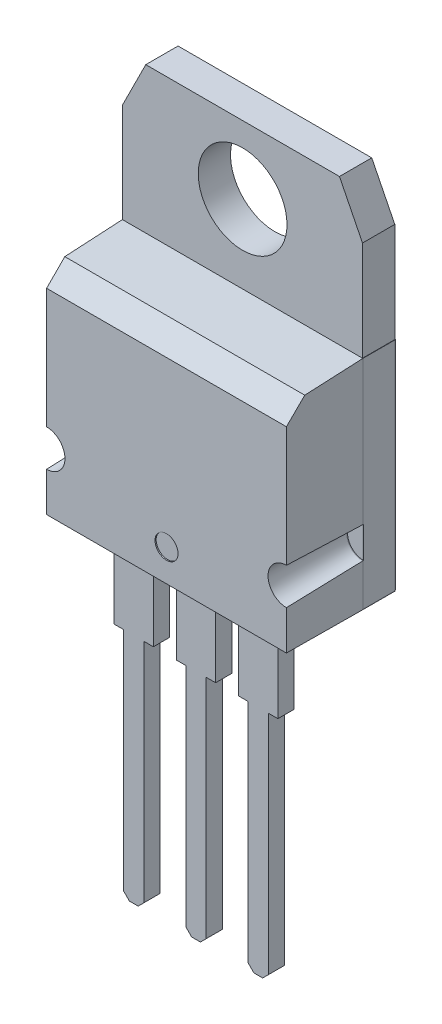
SolidWorks part; units mm, degrees
ref_plane "Front Plane" through (0, 0, 0) normal (0, 0, 1) x (1, 0, 0)
ref_plane "Top Plane" through (0, 0, 0) normal (0, 1, 0) x (1, 0, 0)
ref_plane "Right Plane" through (0, 0, 0) normal (1, 0, 0) x (0, 0, -1)
sketch "Sketch1" plane through (0, 0, 0) normal (0, 0, 1) x (1, 0, 0)
  line L0 (-5.2, 8.9352) -> (-4.2, 10.9352)
  line L1 (-4.2, 10.9352) -> (4.2, 10.9352)
  line L2 (-5.2, 8.9352) -> (-5.2, -4.8148)
  line L3 (-5.2, -4.8148) -> (5.2, -4.8148)
  line L4 (5.2, 8.9352) -> (5.2, -4.8148)
  line L5 (4.2, 10.9352) -> (5.2, 8.9352)
  circle A0 centre (0, 7.9852) radius 1.925
  point P0 (0, 0)
  point P2 (-5.2, 10.9352)
  point P4 (5.2, 10.9352)
  point P12 (0, -4.8148)
  dimension "D1" = 3.85
  dimension "D2" = 10.4
  dimension "D3" = 2.95
  dimension "D4" = 15.75
  dimension "D5" = 1
  dimension "D6" = 2
  dimension "D7" = 1
  dimension "D8" = 2
extrude "Boss-Extrude1" add sketch "Sketch1" along normal blind 1.4
sketch "Sketch2" plane through (0, 0, 1.4) normal (0, 0, 1) x (1, 0, 0)
  line L0 (5.2, -4.8148) -> (5.2, 8.9352) construction
  line L1 (-5.2, -4.8148) -> (5.2, -4.8148)
  line L2 (-5.2, -4.8148) -> (-5.2, 4.4352)
  line L3 (-5.2, 4.4352) -> (5.2, 4.4352)
  line L4 (5.2, -4.8148) -> (5.2, 4.4352)
  dimension "D1" = 9.25
extrude "Boss-Extrude2" add sketch "Sketch2" along normal blind 3.3 separate body
chamfer "Chamfer1" distance 0.75 angle 45 1 edges at (0, 4.4352, 4.7)
draft "Draft7" type of draft neutral plane draft angle 3 faces to draft 1 face at (0, 4.4352, 2.675) neutral plane through (0, 0, 4.7) neutral plane normal (0, 0, 1) parameters "D1"=3
draft "Draft8" type of draft neutral plane draft angle 0.25 faces to draft 2 face at (5.2, 0.6281, 3.2217) face at (-5.2, 0.6281, 3.2217) neutral plane through (0, 0, 4.7) neutral plane normal (0, 0, 1) parameters "D1"=0.25
sketch "Sketch4" plane through (0, 0, 1.4) normal (0, 0, -1) x (-1, 0, 0)
  line L0 (5.2144, -4.8148) -> (-5.2144, -4.8148) construction
  line L1 (-5.2144, 4.6082) -> (-5.2, 4.6082)
  line L2 (-5.2144, 4.6082) -> (-5.2144, -4.8148)
  line L3 (-5.2144, -4.8148) -> (-5.2, -4.8148)
  line L4 (-5.2, 4.6082) -> (-5.2, -4.8148)
  line L5 (5.2144, 4.6082) -> (5.2, 4.6082)
  line L6 (5.2144, 4.6082) -> (5.2144, -4.8148)
  line L7 (5.2144, -4.8148) -> (5.2, -4.8148)
  line L8 (5.2, 4.6082) -> (5.2, -4.8148)
  line L9 (5.2, 8.9352) -> (5.2, -4.8148) construction
extrude "Boss-Extrude4" add sketch "Sketch4" along normal up to surface (1.4 mm away) separate body up to face at (0, 5.0186, 0)
sketch "Sketch5" plane through (0, 0, 4.7) normal (0, 0, 1) x (1, 0, 0)
  line L0 (-5.2, 3.6852) -> (-5.2, -4.8148) construction
  line L1 (-5.2, -4.8148) -> (5.2, -4.8148) construction
  line L2 (0, -4.8148) -> (0, -1.5006) construction
  circle A0 centre (-5.2, -2.3148) radius 0.7956
  circle A1 centre (5.2, -2.3148) radius 0.7956
  dimension "D1" = 2.5
extrude "Cut-Extrude1" cut sketch "Sketch5" against normal blind 3.33 draft 2
sketch "Sketch6" plane through (0, 0, 0) normal (0, 0, -1) x (-1, 0, 0)
  line L0 (0, -4.8148) -> (0, 3.5396) construction
  line L1 (5.2, -4.8148) -> (-5.2, -4.8148) construction
  line L2 (-5.2, 4.6082) -> (-2.5164, 4.6082)
  line L3 (5.2, 4.6082) -> (2.5164, 4.6082)
  line L4 (-2.5164, 4.6082) -> (-2.5164, 3.8582)
  line L5 (2.5164, 4.6082) -> (2.5164, 3.8582)
  line L6 (-2.5164, 3.8582) -> (-3.7, 3.8582)
  line L7 (2.5164, 3.8582) -> (3.7, 3.8582)
  line L8 (-3.7, 3.8582) -> (-3.7, -2.2073)
  line L9 (3.7, 3.8582) -> (3.7, -2.2073)
  line L10 (-3.7, -2.2073) -> (-4.45, -2.2073)
  line L11 (3.7, -2.2073) -> (4.45, -2.2073)
  line L12 (-4.45, -2.2073) -> (-4.45, -3.0398)
  line L13 (4.45, -2.2073) -> (4.45, -3.0398)
  line L14 (-4.45, -3.0398) -> (-4.45, -3.0648)
  line L15 (4.45, -3.0398) -> (4.45, -3.0648)
  line L16 (-4.45, -3.0648) -> (-4.3106, -3.0648)
  line L17 (4.45, -3.0648) -> (4.3106, -3.0648)
  line L18 (-4.3106, -3.0648) -> (4.3106, -3.0648)
  line L19 (-5.2, 4.6082) -> (-5.2, -4.8148) construction
  line L20 (-5.2, 4.6082) -> (-5.2, -4.8148)
  line L21 (5.2, 4.6082) -> (5.2, -4.8148)
  line L22 (-5.2, -4.8148) -> (5.2, -4.8148)
  point P23 (0, -3.0648)
  dimension "D1" = 0.75
  dimension "D2" = 1.5
  dimension "D3" = 0.75
  dimension "D4" = 1.75
extrude "Boss-Extrude6" add sketch "Sketch6" along normal blind 0.025 separate body
ref_plane "Plane1" through (0, 0, 2.72) normal (0, 0, -1) x (-1, 0, 0)
sketch "Sketch10" plane through (0, 0, 2.72) normal (0, 0, -1) x (-1, 0, 0)
  line L0 (-0.85, -4.8148) -> (0.85, -4.8148)
  line L1 (-0.85, -4.8148) -> (-0.85, -8.7448)
  line L2 (-0.85, -8.7448) -> (-0.44, -8.7448)
  line L3 (0.85, -4.8148) -> (0.85, -8.7448)
  line L4 (-0.44, -8.7448) -> (-0.44, -18.5648)
  line L5 (-0.19, -18.8148) -> (0.19, -18.8148)
  line L6 (0.44, -18.5648) -> (0.44, -8.7448)
  line L7 (0.44, -8.7448) -> (0.85, -8.7448)
  line L8 (-0.44, -18.5648) -> (-0.19, -18.8148)
  line L9 (0.19, -18.8148) -> (0.44, -18.5648)
  line L10 (1.85, -4.8148) -> (1.85, -8.7448)
  line L11 (1.85, -4.8148) -> (3.55, -4.8148)
  line L12 (3.55, -4.8148) -> (3.55, -8.7448)
  line L13 (3.14, -8.7448) -> (3.55, -8.7448)
  line L14 (1.85, -8.7448) -> (2.26, -8.7448)
  line L15 (2.26, -8.7448) -> (2.26, -18.5648)
  line L16 (3.14, -18.5648) -> (3.14, -8.7448)
  line L17 (2.26, -18.5648) -> (2.51, -18.8148)
  line L18 (2.51, -18.8148) -> (2.89, -18.8148)
  line L19 (2.89, -18.8148) -> (3.14, -18.5648)
  line L20 (-3.55, -4.8148) -> (-3.55, -8.7448)
  line L21 (-3.55, -4.8148) -> (-1.85, -4.8148)
  line L22 (-1.85, -4.8148) -> (-1.85, -8.7448)
  line L23 (-3.55, -8.7448) -> (-3.14, -8.7448)
  line L24 (-2.26, -8.7448) -> (-1.85, -8.7448)
  line L25 (-2.26, -18.5648) -> (-2.26, -8.7448)
  line L26 (-3.14, -8.7448) -> (-3.14, -18.5648)
  line L27 (-3.14, -18.5648) -> (-2.89, -18.8148)
  line L28 (-2.89, -18.8148) -> (-2.51, -18.8148)
  line L29 (-2.51, -18.8148) -> (-2.26, -18.5648)
  line L41 (0, -4.8148) -> (0, -6.017) construction
  line L42 (5.2, -4.8148) -> (-5.2, -4.8148) construction
  point P6 (-0.44, -18.8148)
  point P8 (0.44, -18.8148)
  point P47 (0, -4.8148)
  dimension "D1" = 1.7
  dimension "D2" = 10.07
  dimension "D3" = 0.88
  dimension "D4" = 2
  dimension "D5" = 0.25
  dimension "D6" = 0.25
  dimension "D7" = 0.25
  dimension "D8" = 0.25
extrude "Boss-Extrude7" add sketch "Sketch10" against normal blind 0.7 separate body
draft "Draft16" type of draft neutral plane draft angle 0.25 faces to draft 1 face at (0, -4.8148, 3.05) neutral plane through (0, 0, 4.7) neutral plane normal (0, 0, 1) parameters "D1"=0.25
sketch "Sketch16" plane through (0, 0, 1.4) normal (0, 0, -1) x (-1, 0, 0)
  line L1 (-5.2144, -4.8148) -> (5.2144, -4.8148)
  line L2 (-5.2144, -4.8148) -> (-5.2144, -4.8292)
  line L3 (-5.2144, -4.8292) -> (5.2144, -4.8292)
  line L4 (5.2144, -4.8148) -> (5.2144, -4.8292)
extrude "Boss-Extrude8" add sketch "Sketch16" along normal up to surface (1.4 mm away) separate body up to face at (0, 5.0186, 0)
sketch "Sketch17" plane through (0, 0, 4.7) normal (0, 0, 1) x (1, 0, 0)
  circle A0 centre (0, -3.4311) radius 0.5
  dimension "D1" = 1
extrude "Cut-Extrude2" cut sketch "Sketch17" against normal blind 0.05
